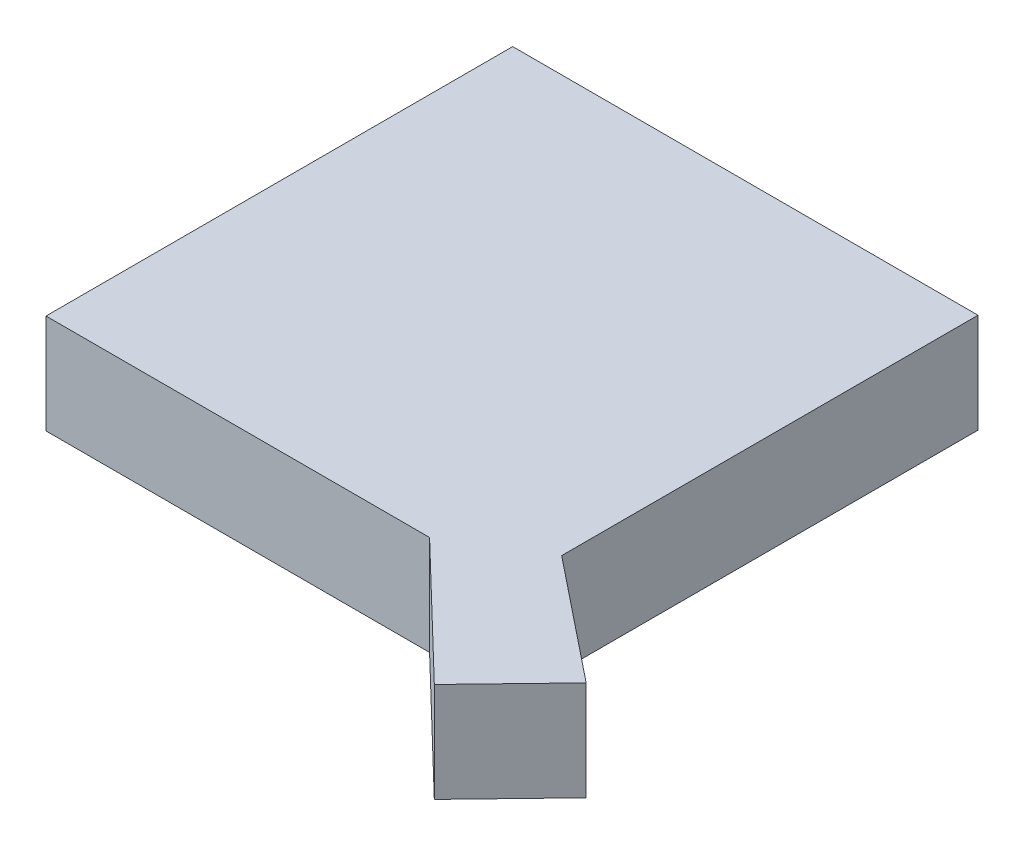
SolidWorks part; units mm, degrees
ref_plane "Front Plane" through (0, 0, 0) normal (0, 0, 1) x (1, 0, 0)
ref_plane "Top Plane" through (0, 0, 0) normal (0, 1, 0) x (1, 0, 0)
ref_plane "Right Plane" through (0, 0, 0) normal (1, 0, 0) x (0, 0, -1)
sketch "Sketch1" plane through (0, 0, 0) normal (0, 1, 0) x (1, 0, 0)
  line L0 (0, 0) -> (0, 46.8815)
  line L1 (0, 46.8815) -> (46.7448, 46.8815)
  line L2 (46.7448, 46.8815) -> (46.7448, 5.0572)
  line L3 (46.7448, 5.0572) -> (59.046, -4.7838)
  line L4 (59.046, -4.7838) -> (51.5617, -12.5524)
  line L5 (51.5617, -12.5524) -> (38.5326, 0)
  line L6 (38.5326, 0) -> (0, 0)
extrude "Boss-Extrude1" add sketch "Sketch1" along normal blind 10
